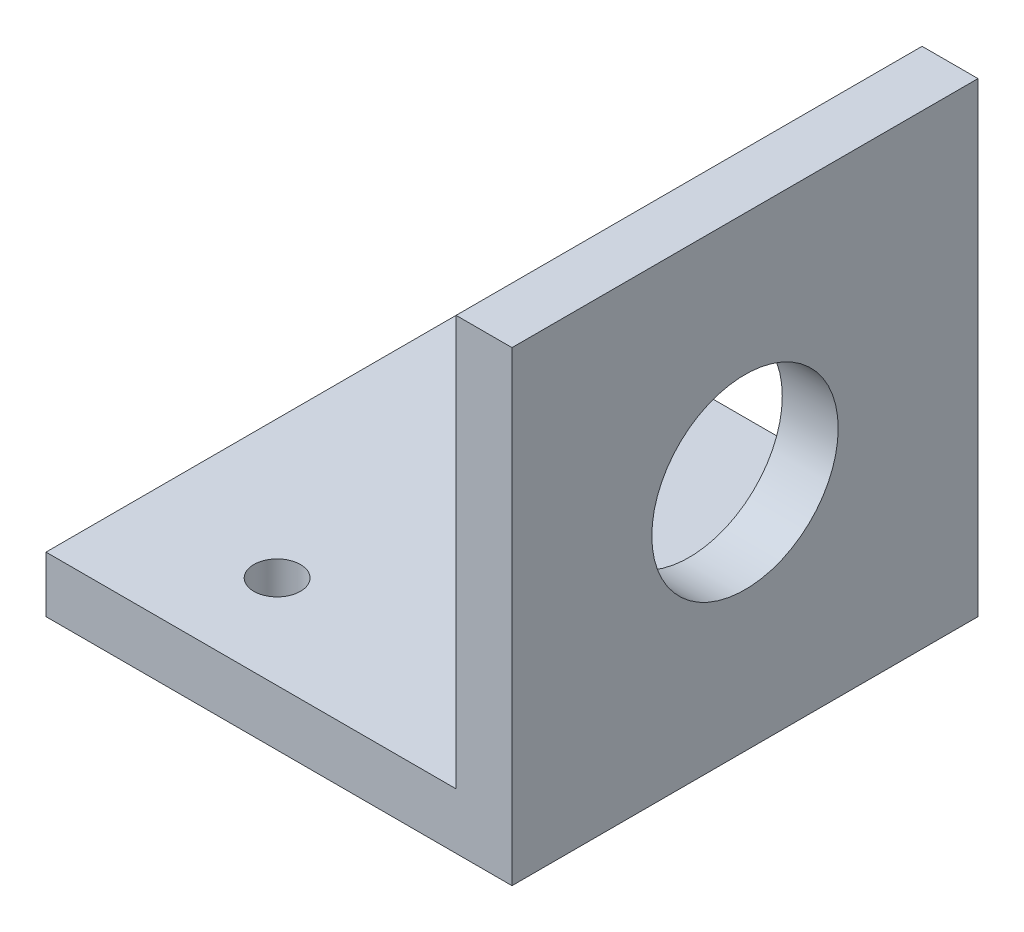
SolidWorks part; units mm, degrees
ref_plane "正面" through (0, 0, 0) normal (0, 0, 1) x (1, 0, 0)
ref_plane "平面" through (0, 0, 0) normal (0, 1, 0) x (1, 0, 0)
ref_plane "右側面" through (0, 0, 0) normal (1, 0, 0) x (0, 0, -1)
sketch "ｽｹｯﾁ1" plane through (0, 0, 0) normal (0, 1, 0) x (1, 0, 0)
  line L1 (-25, 25) -> (25, 25)
  line L2 (-25, 25) -> (-25, -25)
  line L3 (-25, -25) -> (25, -25)
  line L4 (25, 25) -> (25, -25)
  line L5 (-25, 25) -> (25, -25) construction
  line L6 (-25, -25) -> (25, 25) construction
  point P0 (0, 0)
  dimension "D1" = 50
  dimension "D2" = 50
extrude "ﾎﾞｽ - 押し出し1" add sketch "ｽｹｯﾁ1" along normal blind 6
sketch "ｽｹｯﾁ2" plane through (0, 6, 0) normal (0, 1, 0) x (1, 0, 0)
  line L0 (25, -25) -> (19, -25)
  line L1 (-25, -25) -> (25, -25) construction
  line L2 (19, -25) -> (19, 25)
  line L3 (25, 25) -> (-25, 25) construction
  line L4 (19, 25) -> (25, 25)
  line L5 (25, 25) -> (25, -25)
extrude "ﾎﾞｽ - 押し出し2" add sketch "ｽｹｯﾁ2" along normal blind 44
sketch "ｽｹｯﾁ3" plane through (25, 0, 0) normal (1, 0, 0) x (0, 0, -1)
  line L0 (-25, 0) -> (25, 50) construction
  circle A0 centre (0, 25) radius 10
extrude "ｶｯﾄ - 押し出し1" cut sketch "ｽｹｯﾁ3" against normal blind 44
sketch "ｽｹｯﾁ4" plane through (0, 0, 0) normal (0, -1, 0) x (1, 0, 0)
  line L0 (-25, -25) -> (-10.2, -25)
  line L1 (25, -25) -> (-25, -25) construction
  line L2 (-10.2, -25) -> (-10.2, 25) construction
  line L3 (-25, 25) -> (25, 25) construction
  line L4 (-10.2, 15) -> (-10.2, -15)
  circle A0 centre (-10.2, -15) radius 2.5
  circle A1 centre (-10.2, 15) radius 2.5
  point P11 (-10.2, 0)
  dimension "D1" = 14.8
extrude "ｶｯﾄ - 押し出し2" cut sketch "ｽｹｯﾁ4" against normal blind 44 contours L2 L4 A1 | L4 L2 A1 | L2 A0 L4 | A0 L2 L4
